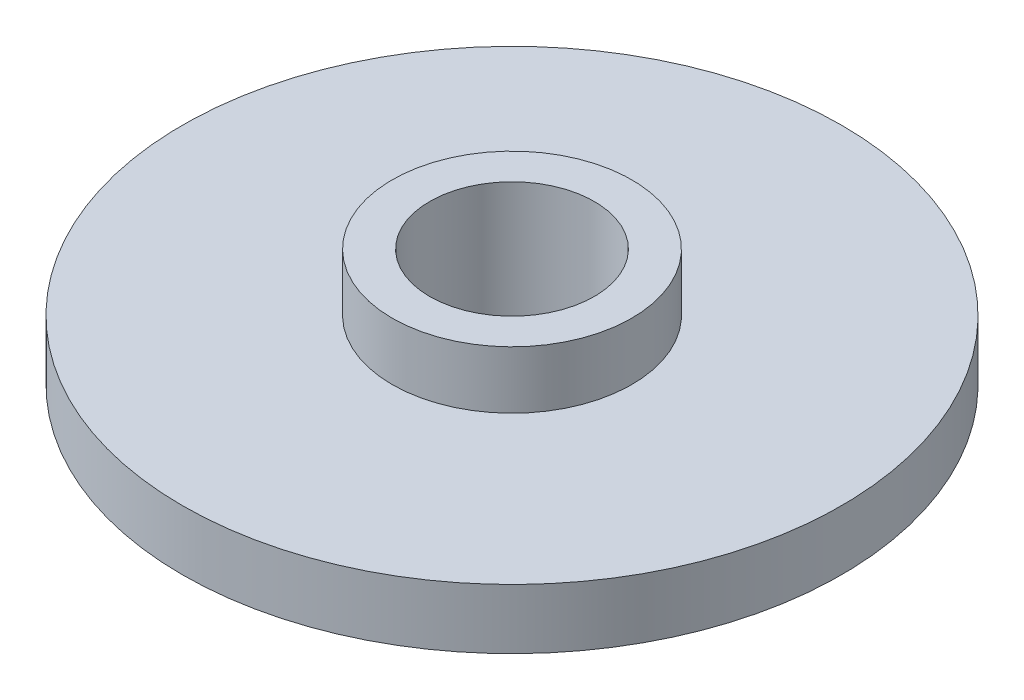
SolidWorks part; units mm, degrees
ref_plane "Front Plane" through (0, 0, 0) normal (0, 0, 1) x (1, 0, 0)
ref_plane "Top Plane" through (0, 0, 0) normal (0, 1, 0) x (1, 0, 0)
ref_plane "Right Plane" through (0, 0, 0) normal (1, 0, 0) x (0, 0, -1)
sketch "Sketch1" plane through (0, 0, 0) normal (0, 1, 0) x (1, 0, 0)
  circle A0 centre (0, 0) radius 5.5
  dimension "D1" = 11
extrude "Boss-Extrude1" add sketch "Sketch1" along normal blind 1
sketch "Sketch2" plane through (0, 1, 0) normal (0, 1, 0) x (1, 0, 0)
  circle A0 centre (0, 0) radius 2
  dimension "D1" = 4
extrude "Boss-Extrude2" add sketch "Sketch2" along normal blind 0.96
sketch "Sketch3" plane through (0, 1.96, 0) normal (0, 1, 0) x (1, 0, 0)
  circle A0 centre (0, 0) radius 1.3743
extrude "Cut-Extrude1" cut sketch "Sketch3" against normal blind 6.96
